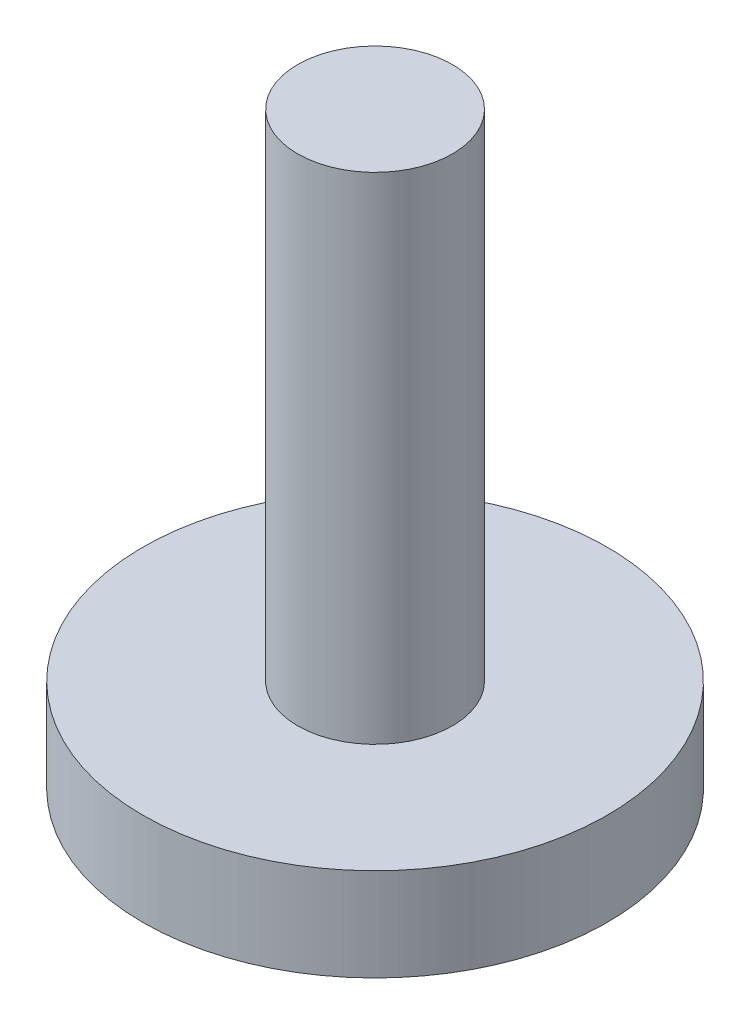
SolidWorks part; units mm, degrees
ref_plane "Front Plane" through (0, 0, 0) normal (0, 0, 1) x (1, 0, 0)
ref_plane "Top Plane" through (0, 0, 0) normal (0, 1, 0) x (1, 0, 0)
ref_plane "Right Plane" through (0, 0, 0) normal (1, 0, 0) x (0, 0, -1)
sketch "Sketch2" plane through (0, 0, 0) normal (0, 1, 0) x (1, 0, 0)
  circle A0 centre (0, 0) radius 7.5
  dimension "D1" = 15
extrude "Boss-Extrude1" add sketch "Sketch2" along normal blind 3
sketch "Sketch5" plane through (0, 3, 0) normal (0, 1, 0) x (1, 0, 0)
  circle A0 centre (0, 0) radius 2.5
  dimension "D1" = 5
extrude "Boss-Extrude2" add sketch "Sketch5" along normal blind 16 contours A0
